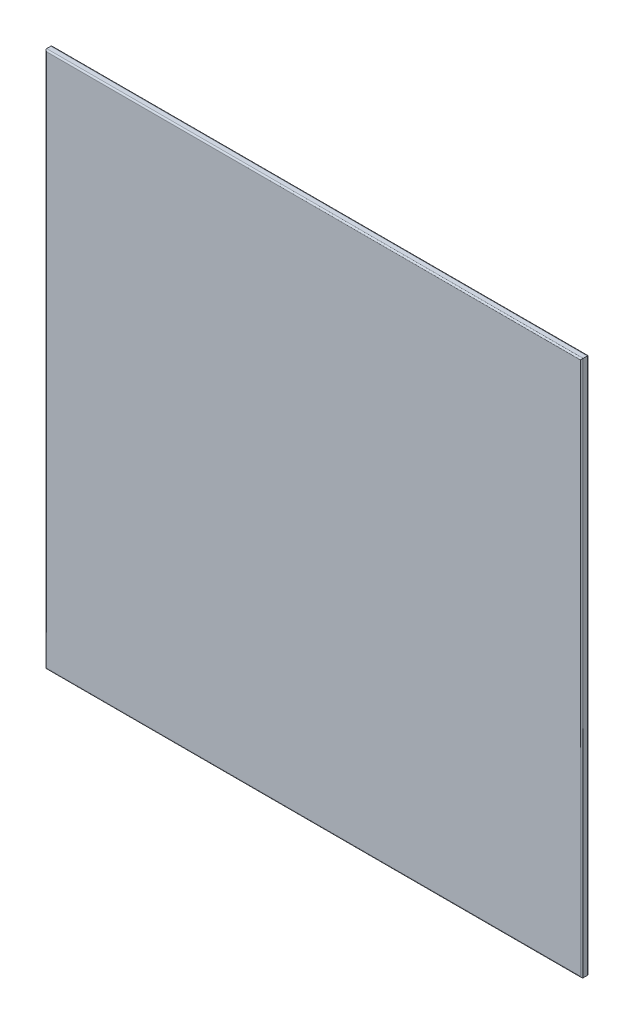
SolidWorks part; units mm, degrees
ref_plane "Front Plane" through (0, 0, 0) normal (0, 0, 1) x (1, 0, 0)
ref_plane "Top Plane" through (0, 0, 0) normal (0, 1, 0) x (1, 0, 0)
ref_plane "Right Plane" through (0, 0, 0) normal (1, 0, 0) x (0, 0, -1)
sketch "Sketch1" plane through (0, 0, 0) normal (0, 0, 1) x (1, 0, 0)
  line L1 (5, 5) -> (1145, 5)
  line L2 (5, 5) -> (5, 1145)
  line L3 (5, 1145) -> (1145, 1145)
  line L4 (1145, 5) -> (1145, 1145)
extrude "Boss-Extrude1" add sketch "Sketch1" along normal blind 15
fillet "Fillet1" radius 3 8 edges at (575, 5, 0) (1145, 575, 0) (575, 1145, 0) (5, 575, 0) (575, 1145, 15) (1145, 575, 15) (575, 5, 15) (5, 575, 15)
